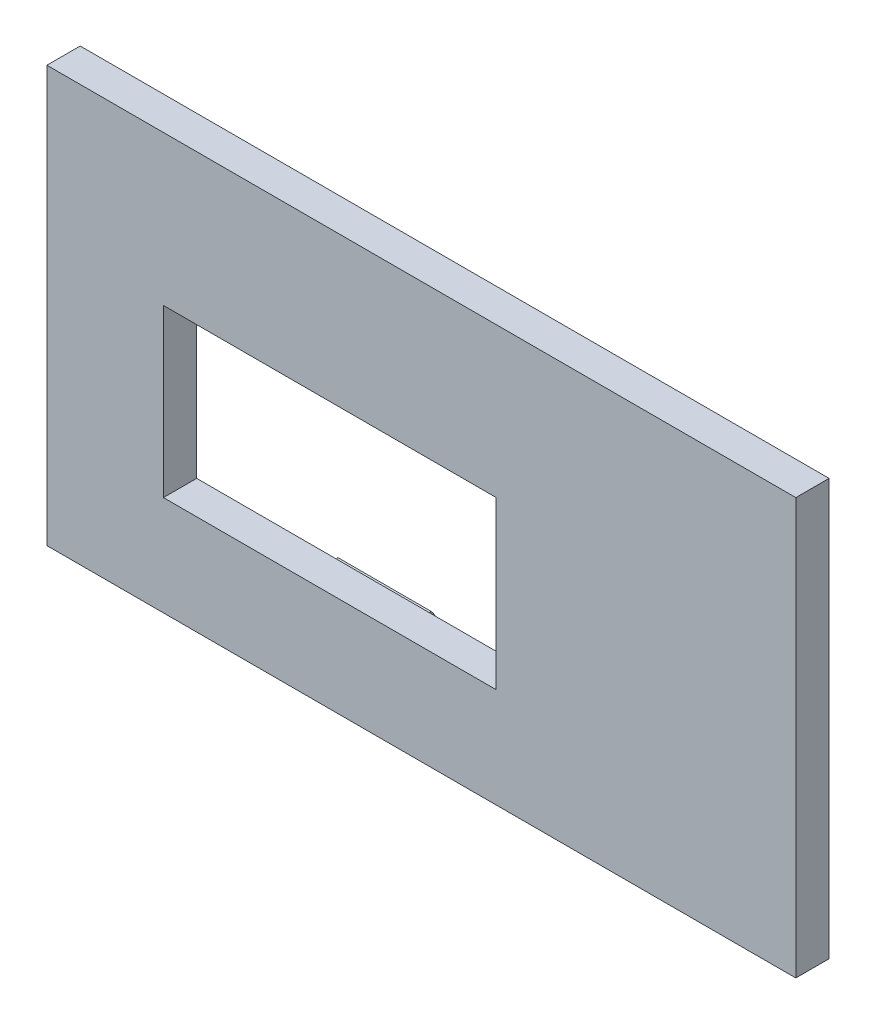
SolidWorks part; units mm, degrees
ref_plane "Ön Düzlem" through (0, 0, 0) normal (0, 0, 1) x (1, 0, 0)
ref_plane "Üst Düzlem" through (0, 0, 0) normal (0, 1, 0) x (1, 0, 0)
ref_plane "Sağ Düzlem" through (0, 0, 0) normal (1, 0, 0) x (0, 0, -1)
sketch "Çizim1" plane through (0, 0, 0) normal (0, 0, 1) x (1, 0, 0)
  line L0 (-22.5, 13.5) -> (22.5, 13.5)
  line L2 (-22.5, 11.5) -> (-22.5, -11.5)
  line L3 (-22.5, -11.5) -> (22.5, -11.5)
  line L4 (22.5, 11.5) -> (22.5, -11.5)
  line L5 (-22.5, 11.5) -> (22.5, -11.5) construction
  line L6 (-22.5, -11.5) -> (22.5, 11.5) construction
  line L10 (-22.5, 11.5) -> (-22.5, 13.5)
  line L11 (22.5, 11.5) -> (22.5, 13.5)
  line L12 (-24.5, 13.5) -> (24.5, 13.5) construction
  line L13 (-24.5, 13.5) -> (-24.5, -13.5) construction
  line L14 (-24.5, -13.5) -> (24.5, -13.5) construction
  line L15 (24.5, 13.5) -> (24.5, -13.5) construction
  line L16 (-22.5, 11.5) -> (-22.5, 13.5)
  line L17 (22.5, 11.5) -> (22.5, 13.5)
  line L19 (-22.5, 11.5) -> (22.5, 11.5) construction
  point P0 (0, 0)
  dimension "D1" = 45
  dimension "D2" = 23
  dimension "D3" = 2
extrude "Yükseklik-Ekstrüzyon1" add sketch "Çizim1" along normal blind 10 contours L4 L11 L0 L10 L2 L3
shell "İç Boşaltma1" thickness 2
sketch "Çizim2" plane through (0, 0, 0) normal (0, 0, 1) x (1, 0, 0)
  line L4 (22.5, -11.5) -> (22.5, 13.5)
  line L5 (-22.5, -11.5) -> (22.5, -11.5)
  line L6 (-22.5, 13.5) -> (-22.5, -11.5)
  line L7 (22.5, 13.5) -> (-22.5, 13.5)
  line L8 (22.5, -11.5) -> (22.5, 13.5)
  line L9 (-22.5, -11.5) -> (22.5, -11.5)
  line L10 (-22.5, 13.5) -> (-22.5, -11.5)
  line L11 (22.5, 13.5) -> (-22.5, 13.5)
  dimension "D1" = 0
extrude "Kes-Ekstrüzyon1" cut sketch "Çizim2" along normal up to surface (8 mm away) up to face at (0, 0, 8)
sketch "Çizim3" plane through (0, 0, 8) normal (0, 0, -1) x (-1, 0, 0)
  line L0 (22.5, 11.5) -> (-22.5, 11.5) construction
  line L1 (-4.5, 4.5) -> (15.5, 4.5)
  line L2 (-4.5, 4.5) -> (-4.5, -5.5)
  line L3 (-4.5, -5.5) -> (15.5, -5.5)
  line L4 (15.5, 4.5) -> (15.5, -5.5)
  line L5 (-4.5, 4.5) -> (15.5, -5.5) construction
  line L6 (-4.5, -5.5) -> (15.5, 4.5) construction
  line L7 (22.5, -11.5) -> (22.5, 13.5) construction
  point P0 (5.5, -0.5)
  dimension "D1" = 17
  dimension "D2" = 10
  dimension "D3" = 20
  dimension "D4" = 7
extrude "Kes-Ekstrüzyon2" cut sketch "Çizim3" against normal blind 6
sketch "Çizim4" plane through (0, 0, 8) normal (0, 0, -1) x (-1, 0, 0)
  line L0 (-20.6088, -8.5) -> (8.0901, -8.5)
  line L10 (-6.5, -7.5) -> (8.0901, -7.5)
  line L12 (8.0901, 8.5) -> (-8.5, 8.5)
  line L17 (-20.6088, 7.5) -> (-20.6088, 8.5)
  line L18 (-20.6088, 8.5) -> (-8.5, 8.5)
  line L19 (-6.5, -7.5) -> (-20.6088, -7.5)
  line L20 (-20.6088, -7.5) -> (-20.6088, -8.5)
  line L22 (8.0901, 8.5) -> (8.0901, 7.5)
  line L23 (-8.5, 8.5) -> (-8.5, -9.5) construction
  line L24 (-6.5, 6.5) -> (-6.5, -7.5) construction
  line L25 (17.5, -7.5) -> (17.5, 6.5) construction
  line L26 (19.5, -9.5) -> (19.5, 8.5) construction
  line L27 (8.0901, -7.5) -> (8.0901, -8.5)
  line L28 (-6.5, -7.5) -> (17.5, -7.5) construction
  line L29 (-8.5, -9.5) -> (19.5, -9.5) construction
  line L30 (17.5, 6.5) -> (-6.5, 6.5) construction
  line L31 (19.5, 8.5) -> (-8.5, 8.5) construction
  line L32 (-20.6088, 7.5) -> (8.0901, 7.5)
  dimension "D1" = 2
revolve "Kes-Döndür1" cut sketch "Çizim4" angle 360 about L32
sketch "Çizim6" plane through (-8.0901, 0, 0) normal (1, 0, 0) x (0, 0, -1)
  line L0 (-8, 9) -> (-8, 8.5)
  line L1 (-8, 6.5) -> (-8, 8.5)
  line L4 (-7.2929, 6.7929) -> (-6.9393, 6.4393)
  line L5 (-8, 8.5) -> (-8, 6.5) construction
  arc A0 (-6.9393, 6.4393) -> (-8, 9) centre (-8, 7.5) ccw
  arc A1 (-8, 8.5) -> (-8, 6.5) centre (-8, 7.5) ccw
  arc A2 (-7.2929, 6.7929) -> (-8, 8.5) centre (-8, 7.5) ccw
  circle A3 centre (-8, 7.5) radius 1.5 construction
  circle A4 centre (-8, 7.5) radius 1 construction
  dimension "D3" = 45
  dimension "D1" = 0
  dimension "D2" = 0.5
extrude "Yükseklik-Ekstrüzyon2" add sketch "Çizim6" along normal up to surface (28.699 mm away) up to face at (20.6088, 7.5, 8.5)
sketch "Çizim8" plane through (0, 0, 0) normal (1, 0, 0) x (0, 0, -1)
  line L2 (-7.2929, 6.7929) -> (-6.9393, 6.4393)
  line L3 (-8, 9) -> (-8, 8.5)
  line L4 (-7.2929, 6.7929) -> (-6.9393, 6.4393)
  line L5 (-8, 9) -> (-8, 8.5)
  arc A2 (-6.9393, 6.4393) -> (-8, 9) centre (-8, 7.5) ccw
  arc A3 (-7.2929, 6.7929) -> (-8, 8.5) centre (-8, 7.5) ccw
  arc A4 (-6.9393, 6.4393) -> (-8, 9) centre (-8, 7.5) ccw
  arc A5 (-7.2929, 6.7929) -> (-8, 8.5) centre (-8, 7.5) ccw
  dimension "D1" = 0
extrude "Kes-Ekstrüzyon3" cut sketch "Çizim8" against normal mid plane 5
mirror "Aynalama1" about plane through (0, 0, 0) normal (0, 1, 0) of "Kes-Ekstrüzyon3", "Yükseklik-Ekstrüzyon2", "Kes-Döndür1"
ref_plane "Düzlem1" through (0, 0, 9) normal (0, 0, 1) x (1, 0, 0)
